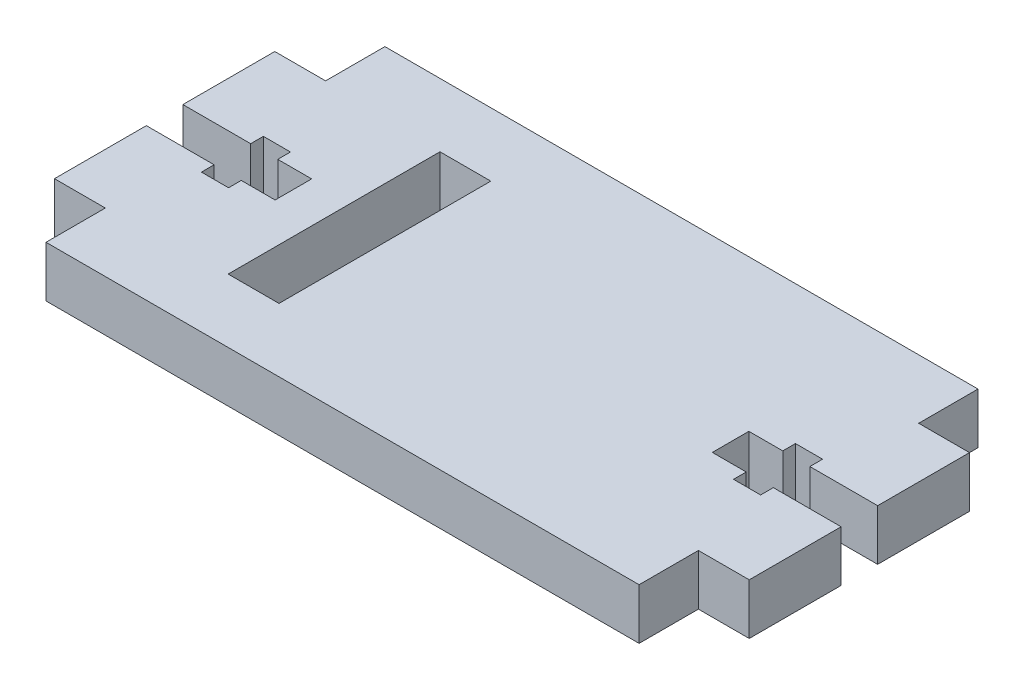
SolidWorks part; units mm, degrees
ref_plane "Front Plane" through (0, 0, 0) normal (0, 0, 1) x (1, 0, 0)
ref_plane "Top Plane" through (0, 0, 0) normal (0, 1, 0) x (1, 0, 0)
ref_plane "Right Plane" through (0, 0, 0) normal (1, 0, 0) x (0, 0, -1)
sketch "Sketch1" plane through (0, 0, 0) normal (0, 1, 0) x (1, 0, 0)
  line L0 (41, -13) -> (41, -2.1566) construction
  line L1 (-35, 20) -> (35, 20)
  line L2 (-35, 20) -> (-35, 13)
  line L3 (-35, -20) -> (35, -20)
  line L4 (35, 20) -> (35, 13)
  line L5 (-35, 20) -> (35, -20) construction
  line L6 (-35, -20) -> (35, 20) construction
  line L7 (35, 0) -> (-18, 0) construction
  line L8 (35, -20) -> (35, -13) construction
  line L9 (-21, 12.5) -> (-15, 12.5)
  line L10 (-21, 12.5) -> (-21, -12.5)
  line L11 (-21, -12.5) -> (-15, -12.5)
  line L12 (-15, 12.5) -> (-15, -12.5)
  line L13 (-21, 12.5) -> (-15, -12.5) construction
  line L14 (-21, -12.5) -> (-15, 12.5) construction
  line L15 (35, -13) -> (41, -13)
  line L16 (41, -13) -> (41, -2.1566)
  line L17 (41, 13) -> (35, 13)
  line L18 (0, 20) -> (0, -20) construction
  line L19 (-41, -13) -> (-41, -2.1566)
  line L20 (-35, -13) -> (-41, -13)
  line L21 (-41, 13) -> (-35, 13)
  line L22 (35, -13) -> (35, -20)
  line L23 (-35, -13) -> (-35, -20)
  line L24 (41, -2.1566) -> (33, -2.1566)
  line L25 (33, -2.1566) -> (33, -3.6566)
  line L26 (33, -3.6566) -> (29.8, -3.6566)
  line L27 (29.8, -3.6566) -> (29.8, -2.1566)
  line L28 (29.8, -2.1566) -> (25.8, -2.1566)
  line L29 (25.8, -2.1566) -> (25.8, 1.8434)
  line L30 (25.8, 2.1566) -> (25.8, -1.8434)
  line L31 (29.8, 2.1566) -> (25.8, 2.1566)
  line L32 (29.8, 3.6566) -> (29.8, 2.1566)
  line L33 (33, 3.6566) -> (29.8, 3.6566)
  line L34 (33, 2.1566) -> (33, 3.6566)
  line L35 (41, 2.1566) -> (33, 2.1566)
  line L36 (41, 2.1566) -> (41, 13)
  line L37 (-41, -2.1566) -> (-33, -2.1566)
  line L38 (-33, -2.1566) -> (-33, -3.6566)
  line L39 (-33, -3.6566) -> (-29.8, -3.6566)
  line L40 (-29.8, -3.6566) -> (-29.8, -2.1566)
  line L41 (-29.8, -2.1566) -> (-25.8, -2.1566)
  line L42 (-25.8, -2.1566) -> (-25.8, 1.8434)
  line L43 (-25.8, 2.1566) -> (-25.8, -1.8434)
  line L44 (-29.8, 2.1566) -> (-25.8, 2.1566)
  line L45 (-29.8, 3.6566) -> (-29.8, 2.1566)
  line L46 (-33, 3.6566) -> (-29.8, 3.6566)
  line L47 (-33, 2.1566) -> (-33, 3.6566)
  line L48 (-41, 2.1566) -> (-33, 2.1566)
  line L49 (-41, 2.1566) -> (-41, 13)
  point P0 (0, 0)
  dimension "D1" = 40
  dimension "D2" = 70
  dimension "D3" = 53
  dimension "D4" = 25
  dimension "D5" = 6
  dimension "D6" = 7
  dimension "D7" = 6
  dimension "D8" = 26
  dimension "D9" = 20
extrude "Boss-Extrude1" add sketch "Sketch1" along normal blind 6 contours L49 L48 L47 L46 L45 L44 L43 L42 L41 L40 L39 L38 L37 L19 L20 L23 L3 L22 L15 L16 L24 L25 L26 L27 L28 L29 L30 L31 L32 L33 L34 L35 L36 L17 L4 L1 L2 L21 L9 L12 L11 L10
